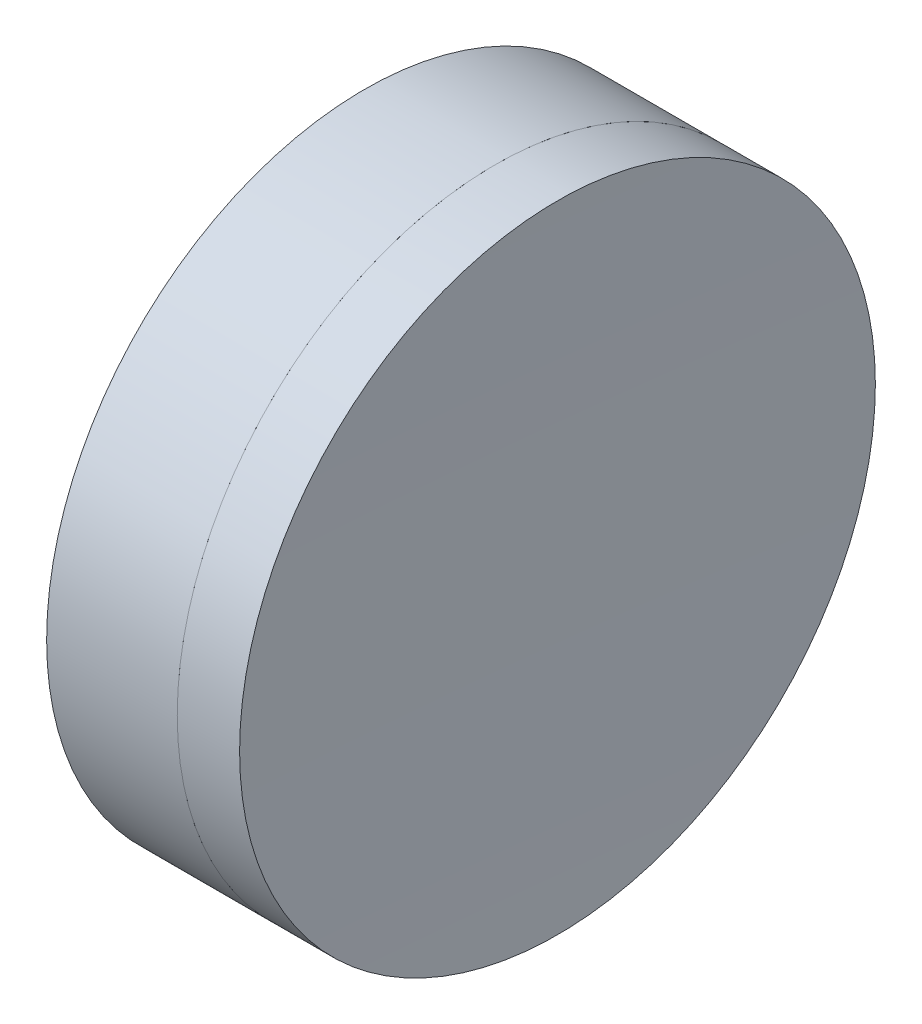
SolidWorks part; units mm, degrees
ref_plane "前视基准面" through (0, 0, 0) normal (0, 0, 1) x (1, 0, 0)
ref_plane "上视基准面" through (0, 0, 0) normal (0, 1, 0) x (1, 0, 0)
ref_plane "右视基准面" through (0, 0, 0) normal (1, 0, 0) x (0, 0, -1)
sketch "草图1" plane through (0, 0, 0) normal (0, 1, 0) x (1, 0, 0)
  line L0 (-0.8161, 0) -> (404.2054, 0) construction
  line L1 (252.1199, 12.7) -> (257.3378, 12.7)
  line L4 (252.1199, -12.7) -> (257.3378, -12.7)
  arc A0 (252.1199, -12.7) -> (252.1199, 12.7) centre (201.6947, 0) ccw
  arc A1 (257.3378, 12.7) -> (257.3378, -12.7) centre (305.5947, 0) ccw
  point P6 (253.6947, 0)
  point P8 (255.6947, 0)
  dimension "D3" = 12.7
  dimension "D4" = 2
  dimension "D1" = 52
  dimension "D5" = 49.9
  dimension "D2" = 12.7
revolve "旋转1" add sketch "草图1" angle 360 about L0
sketch "草图2" plane through (0, 0, 0) normal (0, 1, 0) x (1, 0, 0)
  line L2 (252.1199, 0) -> (272.9951, 0) construction
  line L3 (252.1199, -12.7) -> (252.1199, 12.7) construction
  line L6 (257.3378, 12.7) -> (259.8291, 12.7)
  line L7 (257.3378, -12.7) -> (259.8291, -12.7)
  arc A2 (257.3378, 12.7) -> (257.3378, -12.7) centre (305.5947, 0) ccw construction
  arc A3 (257.3378, 12.7) -> (257.3378, -12.7) centre (305.5947, 0) ccw
  arc A4 (259.8291, 12.7) -> (259.8291, -12.7) centre (859.6947, 0) ccw
  point P8 (255.6947, 0)
  point P9 (259.6947, 0)
  dimension "D1" = 4
  dimension "D2" = 600
revolve "旋转3" add sketch "草图2" angle 360 about L2
